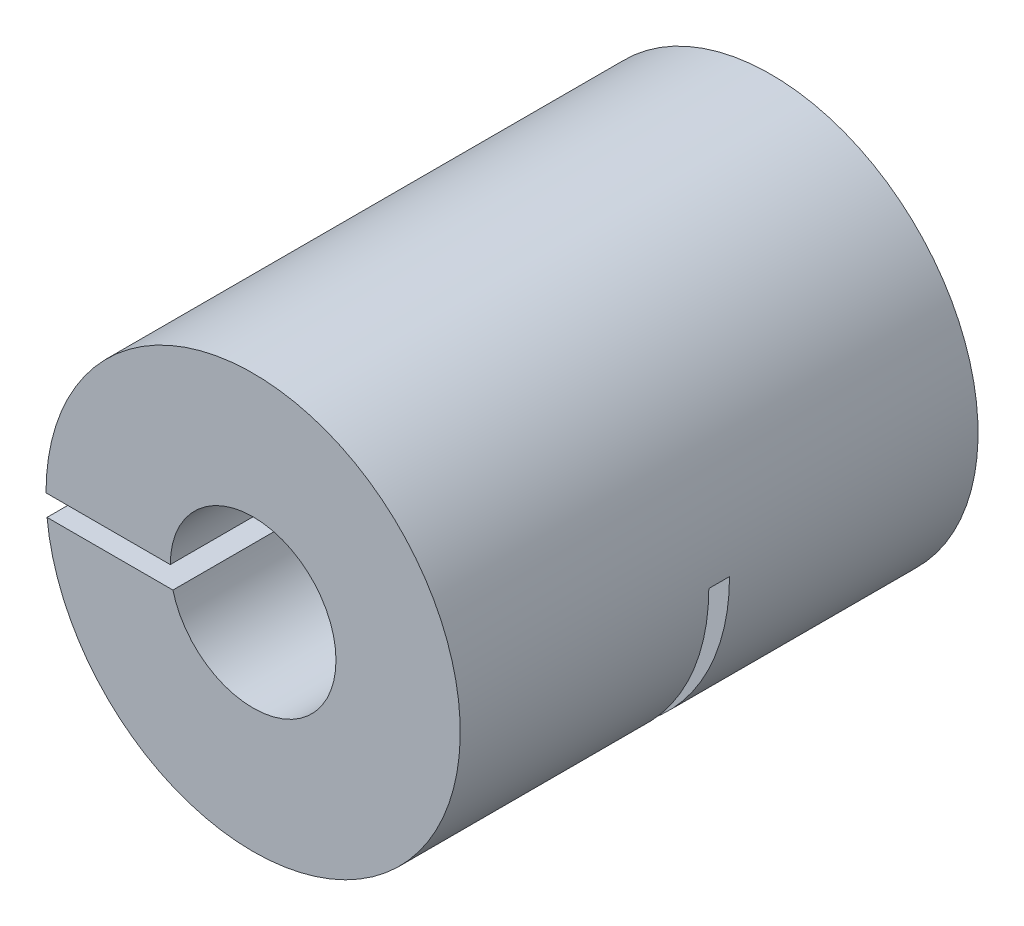
SolidWorks part; units mm, degrees
ref_plane "前视" through (0, 0, 0) normal (0, 0, 1) x (1, 0, 0)
ref_plane "上视" through (0, 0, 0) normal (0, 1, 0) x (1, 0, 0)
ref_plane "右视" through (0, 0, 0) normal (1, 0, 0) x (0, 0, -1)
sketch "草图1" plane through (0, 0, 0) normal (0, 0, 1) x (1, 0, 0)
  circle A0 centre (0, 0) radius 10
  dimension "D1" = 20
extrude "凸台-拉伸1" add sketch "草图1" against normal mid plane 25
sketch "草图2" plane through (0, 0, 12.5) normal (0, 0, 1) x (1, 0, 0)
  circle A0 centre (0, 0) radius 4
  dimension "D1" = 8
extrude "切除-拉伸1" cut sketch "草图2" against normal blind 12.5
sketch "草图4" plane through (0, 0, 0) normal (0, 1, 0) x (1, 0, 0)
  line L1 (-26.5246, 0.5) -> (26.5246, 0.5)
  line L2 (-26.5246, 0.5) -> (-26.5246, -0.5)
  line L3 (-26.5246, -0.5) -> (26.5246, -0.5)
  line L4 (26.5246, 0.5) -> (26.5246, -0.5)
  line L5 (-26.5246, 0.5) -> (26.5246, -0.5) construction
  line L6 (-26.5246, -0.5) -> (26.5246, 0.5) construction
  point P0 (0, 0)
  dimension "D1" = 1
extrude "切除-拉伸2" cut sketch "草图4" against normal blind 25
sketch "草图5" plane through (0, 0, 12.5) normal (0, 0, 1) x (1, 0, 0)
  line L1 (0, 0) -> (-15.9036, 0)
  line L2 (0, 0) -> (0, -1)
  line L3 (0, -1) -> (-15.9036, -1)
  line L4 (-15.9036, 0) -> (-15.9036, -1)
  dimension "D1" = 1
extrude "切除-拉伸3" cut sketch "草图5" against normal blind 25
sketch "草图6" plane through (0, 0, -12.5) normal (0, 0, -1) x (-1, 0, 0)
  circle A0 centre (0, 0) radius 2.5
extrude "切除-拉伸4" cut sketch "草图6" against normal blind 25
